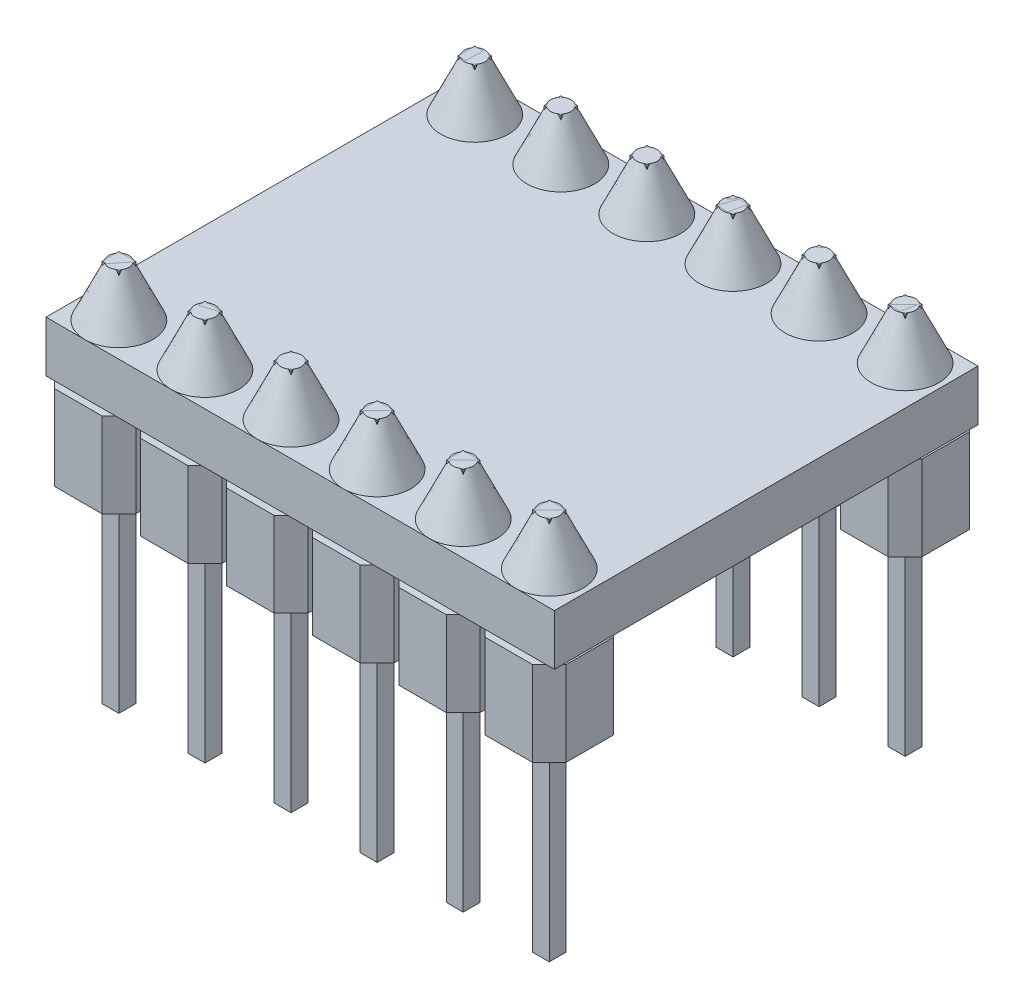
SolidWorks part; units mm, degrees
ref_plane "Front Plane" through (0, 0, 0) normal (0, 0, 1) x (1, 0, 0)
ref_plane "Top Plane" through (0, 0, 0) normal (0, 1, 0) x (1, 0, 0)
ref_plane "Right Plane" through (0, 0, 0) normal (1, 0, 0) x (0, 0, -1)
sketch "Sketch1" plane through (0, 0, 0) normal (0, 1, 0) x (1, 0, 0)
  line L1 (7.5, -6.25) -> (-7.5, -6.25)
  line L2 (7.5, -6.25) -> (7.5, 6.25)
  line L3 (7.5, 6.25) -> (-7.5, 6.25)
  line L4 (-7.5, -6.25) -> (-7.5, 6.25)
  line L5 (7.5, -6.25) -> (-7.5, 6.25) construction
  line L6 (7.5, 6.25) -> (-7.5, -6.25) construction
  point P0 (0, 0)
  dimension "D1" = 12.5
  dimension "D2" = 15
extrude "pcb" add sketch "Sketch1" along normal blind 1.5
sketch "Sketch2" plane through (0, 1.5, 0) normal (0, 1, 0) x (1, 0, 0)
  line L0 (-7.5, 5.25) -> (7.5, 5.25) construction
  line L1 (-7.5, 6.25) -> (-7.5, -6.25) construction
  line L2 (7.5, -6.25) -> (7.5, 6.25) construction
  line L3 (7.5, 6.25) -> (-7.5, 6.25) construction
  line L4 (-6.1, 5) -> (-6.6, 5)
  line L5 (-6.1, 5) -> (-6.1, 5.5)
  line L6 (-6.1, 5.5) -> (-6.6, 5.5)
  line L7 (-6.6, 5) -> (-6.6, 5.5)
  line L8 (-6.1, 5) -> (-6.6, 5.5) construction
  line L9 (-6.1, 5.5) -> (-6.6, 5) construction
  line L10 (-0.825, 0) -> (0.825, 0) construction
  line L11 (-6.1, -5.5) -> (-6.6, -5.5)
  line L12 (-6.6, -5) -> (-6.6, -5.5)
  line L13 (-6.1, -5) -> (-6.6, -5)
  line L14 (-6.1, -5) -> (-6.1, -5.5)
  line L15 (-3.56, 5) -> (-3.56, 5.5)
  line L16 (-3.56, 5) -> (-4.06, 5)
  line L17 (-4.06, 5) -> (-4.06, 5.5)
  line L18 (-3.56, 5.5) -> (-4.06, 5.5)
  line L19 (-3.56, -5.5) -> (-4.06, -5.5)
  line L20 (-4.06, -5) -> (-4.06, -5.5)
  line L21 (-3.56, -5) -> (-4.06, -5)
  line L22 (-3.56, -5) -> (-3.56, -5.5)
  line L23 (-1.02, 5) -> (-1.02, 5.5)
  line L24 (-1.02, 5) -> (-1.52, 5)
  line L25 (-1.52, 5) -> (-1.52, 5.5)
  line L26 (-1.02, 5.5) -> (-1.52, 5.5)
  line L27 (-1.02, -5.5) -> (-1.52, -5.5)
  line L28 (-1.52, -5) -> (-1.52, -5.5)
  line L29 (-1.02, -5) -> (-1.52, -5)
  line L30 (-1.02, -5) -> (-1.02, -5.5)
  line L31 (1.52, 5) -> (1.52, 5.5)
  line L32 (1.52, 5) -> (1.02, 5)
  line L33 (1.02, 5) -> (1.02, 5.5)
  line L34 (1.52, 5.5) -> (1.02, 5.5)
  line L35 (1.52, -5.5) -> (1.02, -5.5)
  line L36 (1.02, -5) -> (1.02, -5.5)
  line L37 (1.52, -5) -> (1.02, -5)
  line L38 (1.52, -5) -> (1.52, -5.5)
  line L39 (4.06, 5) -> (4.06, 5.5)
  line L40 (4.06, 5) -> (3.56, 5)
  line L41 (3.56, 5) -> (3.56, 5.5)
  line L42 (4.06, 5.5) -> (3.56, 5.5)
  line L43 (4.06, -5.5) -> (3.56, -5.5)
  line L44 (3.56, -5) -> (3.56, -5.5)
  line L45 (4.06, -5) -> (3.56, -5)
  line L46 (4.06, -5) -> (4.06, -5.5)
  line L47 (6.6, 5) -> (6.6, 5.5)
  line L48 (6.6, 5) -> (6.1, 5)
  line L49 (6.1, 5) -> (6.1, 5.5)
  line L50 (6.6, 5.5) -> (6.1, 5.5)
  line L51 (6.6, -5.5) -> (6.1, -5.5)
  line L52 (6.1, -5) -> (6.1, -5.5)
  line L53 (6.6, -5) -> (6.1, -5)
  line L54 (6.6, -5) -> (6.6, -5.5)
  line L55 (-6.1, 5) -> (-3.56, 5) construction
  point P6 (-6.35, 5.25)
  dimension "D1" = 0.5
  dimension "D2" = 1
  dimension "D4" = 2.54
  dimension "D5" = 1.02
  dimension "D3" = 6
extrude "pins" add sketch "Sketch2" against normal blind 9.8 and the other way blind 1.5 separate body
sketch "Sketch3" plane through (0, 0, 0) normal (0, -1, 0) x (1, 0, 0)
  line L0 (-6.1, 5) -> (-6.6, 5) construction
  line L1 (-5.65, 4.05) -> (-7.05, 4.05)
  line L2 (-5.15, 4.55) -> (-5.15, 5.95)
  line L3 (-5.65, 6.45) -> (-7.05, 6.45)
  line L4 (-7.55, 4.55) -> (-7.55, 5.95)
  line L5 (6.215, 0) -> (-6.215, 0) construction
  line L6 (-5.65, -6.45) -> (-7.05, -6.45)
  line L7 (-6.1, 5.5) -> (-6.1, 5) construction
  line L8 (-5.15, 5.95) -> (-5.65, 6.45)
  line L9 (-7.05, 6.45) -> (-7.55, 5.95)
  line L10 (-7.05, 4.05) -> (-7.55, 4.55)
  line L11 (-5.15, 4.55) -> (-5.65, 4.05)
  line L12 (-7.05, -6.45) -> (-7.55, -5.95)
  line L13 (-7.55, -4.55) -> (-7.55, -5.95)
  line L14 (-7.05, -4.05) -> (-7.55, -4.55)
  line L15 (-5.65, -4.05) -> (-7.05, -4.05)
  line L16 (-5.15, -5.95) -> (-5.65, -6.45)
  line L17 (-5.15, -4.55) -> (-5.65, -4.05)
  line L18 (-5.15, -4.55) -> (-5.15, -5.95)
  line L19 (-2.61, 4.55) -> (-2.61, 5.95)
  line L20 (-2.61, 4.55) -> (-3.11, 4.05)
  line L21 (-2.61, 5.95) -> (-3.11, 6.45)
  line L22 (-3.11, 4.05) -> (-4.51, 4.05)
  line L23 (-4.51, 4.05) -> (-5.01, 4.55)
  line L24 (-5.01, 4.55) -> (-5.01, 5.95)
  line L25 (-4.51, 6.45) -> (-5.01, 5.95)
  line L26 (-3.11, 6.45) -> (-4.51, 6.45)
  line L27 (-3.11, -6.45) -> (-4.51, -6.45)
  line L28 (-4.51, -6.45) -> (-5.01, -5.95)
  line L29 (-5.01, -4.55) -> (-5.01, -5.95)
  line L30 (-4.51, -4.05) -> (-5.01, -4.55)
  line L31 (-3.11, -4.05) -> (-4.51, -4.05)
  line L32 (-2.61, -4.55) -> (-3.11, -4.05)
  line L33 (-2.61, -4.55) -> (-2.61, -5.95)
  line L34 (-2.61, -5.95) -> (-3.11, -6.45)
  line L35 (-0.07, 4.55) -> (-0.07, 5.95)
  line L36 (-0.07, 4.55) -> (-0.57, 4.05)
  line L37 (-0.07, 5.95) -> (-0.57, 6.45)
  line L38 (-0.57, 4.05) -> (-1.97, 4.05)
  line L39 (-1.97, 4.05) -> (-2.47, 4.55)
  line L40 (-2.47, 4.55) -> (-2.47, 5.95)
  line L41 (-1.97, 6.45) -> (-2.47, 5.95)
  line L42 (-0.57, 6.45) -> (-1.97, 6.45)
  line L43 (-0.57, -6.45) -> (-1.97, -6.45)
  line L44 (-1.97, -6.45) -> (-2.47, -5.95)
  line L45 (-2.47, -4.55) -> (-2.47, -5.95)
  line L46 (-1.97, -4.05) -> (-2.47, -4.55)
  line L47 (-0.57, -4.05) -> (-1.97, -4.05)
  line L48 (-0.07, -4.55) -> (-0.57, -4.05)
  line L49 (-0.07, -4.55) -> (-0.07, -5.95)
  line L50 (-0.07, -5.95) -> (-0.57, -6.45)
  line L51 (2.47, 4.55) -> (2.47, 5.95)
  line L52 (2.47, 4.55) -> (1.97, 4.05)
  line L53 (2.47, 5.95) -> (1.97, 6.45)
  line L54 (1.97, 4.05) -> (0.57, 4.05)
  line L55 (0.57, 4.05) -> (0.07, 4.55)
  line L56 (0.07, 4.55) -> (0.07, 5.95)
  line L57 (0.57, 6.45) -> (0.07, 5.95)
  line L58 (1.97, 6.45) -> (0.57, 6.45)
  line L59 (1.97, -6.45) -> (0.57, -6.45)
  line L60 (0.57, -6.45) -> (0.07, -5.95)
  line L61 (0.07, -4.55) -> (0.07, -5.95)
  line L62 (0.57, -4.05) -> (0.07, -4.55)
  line L63 (1.97, -4.05) -> (0.57, -4.05)
  line L64 (2.47, -4.55) -> (1.97, -4.05)
  line L65 (2.47, -4.55) -> (2.47, -5.95)
  line L66 (2.47, -5.95) -> (1.97, -6.45)
  line L67 (5.01, 4.55) -> (5.01, 5.95)
  line L68 (5.01, 4.55) -> (4.51, 4.05)
  line L69 (5.01, 5.95) -> (4.51, 6.45)
  line L70 (4.51, 4.05) -> (3.11, 4.05)
  line L71 (3.11, 4.05) -> (2.61, 4.55)
  line L72 (2.61, 4.55) -> (2.61, 5.95)
  line L73 (3.11, 6.45) -> (2.61, 5.95)
  line L74 (4.51, 6.45) -> (3.11, 6.45)
  line L75 (4.51, -6.45) -> (3.11, -6.45)
  line L76 (3.11, -6.45) -> (2.61, -5.95)
  line L77 (2.61, -4.55) -> (2.61, -5.95)
  line L78 (3.11, -4.05) -> (2.61, -4.55)
  line L79 (4.51, -4.05) -> (3.11, -4.05)
  line L80 (5.01, -4.55) -> (4.51, -4.05)
  line L81 (5.01, -4.55) -> (5.01, -5.95)
  line L82 (5.01, -5.95) -> (4.51, -6.45)
  line L83 (7.55, 4.55) -> (7.55, 5.95)
  line L84 (7.55, 4.55) -> (7.05, 4.05)
  line L85 (7.55, 5.95) -> (7.05, 6.45)
  line L86 (7.05, 4.05) -> (5.65, 4.05)
  line L87 (5.65, 4.05) -> (5.15, 4.55)
  line L88 (5.15, 4.55) -> (5.15, 5.95)
  line L89 (5.65, 6.45) -> (5.15, 5.95)
  line L90 (7.05, 6.45) -> (5.65, 6.45)
  line L91 (7.05, -6.45) -> (5.65, -6.45)
  line L92 (5.65, -6.45) -> (5.15, -5.95)
  line L93 (5.15, -4.55) -> (5.15, -5.95)
  line L94 (5.65, -4.05) -> (5.15, -4.55)
  line L95 (7.05, -4.05) -> (5.65, -4.05)
  line L96 (7.55, -4.55) -> (7.05, -4.05)
  line L97 (7.55, -4.55) -> (7.55, -5.95)
  line L98 (7.55, -5.95) -> (7.05, -6.45)
  line L99 (-5.15, 4.55) -> (-2.61, 4.55) construction
  point P0 (-6.35, 5.25)
  point P7 (-6.35, 5)
  point P10 (-6.1, 5.25)
  dimension "D1" = 6
  dimension "D2" = 2.54
extrude "pin_supports" add sketch "Sketch3" along normal blind 2.5 separate body
sketch "Sketch4" plane through (0, 1.5, 0) normal (0, 1, 0) x (1, 0, 0)
  line L0 (-6.1, -5) -> (-6.6, -5) construction
  line L1 (-6.1, -5.5) -> (-6.1, -5) construction
  line L2 (-6.215, 0) -> (6.215, 0) construction
  line L3 (-6.35, -5.25) -> (-3.81, -5.25) construction
  circle A0 centre (-6.35, -5.25) radius 1
  circle A1 centre (-6.35, 5.25) radius 1
  circle A2 centre (-3.81, -5.25) radius 1
  circle A3 centre (-3.81, 5.25) radius 1
  circle A4 centre (-1.27, -5.25) radius 1
  circle A5 centre (-1.27, 5.25) radius 1
  circle A6 centre (1.27, -5.25) radius 1
  circle A7 centre (1.27, 5.25) radius 1
  circle A8 centre (3.81, -5.25) radius 1
  circle A9 centre (3.81, 5.25) radius 1
  circle A10 centre (6.35, -5.25) radius 1
  circle A11 centre (6.35, 5.25) radius 1
  point P5 (-6.35, -5)
  point P8 (-6.1, -5.25)
  dimension "D1" = 2
  dimension "D3" = 2.54
  dimension "D2" = 6
extrude "solders" add sketch "Sketch4" along normal up to surface (1.5 mm away) draft 25 separate body
